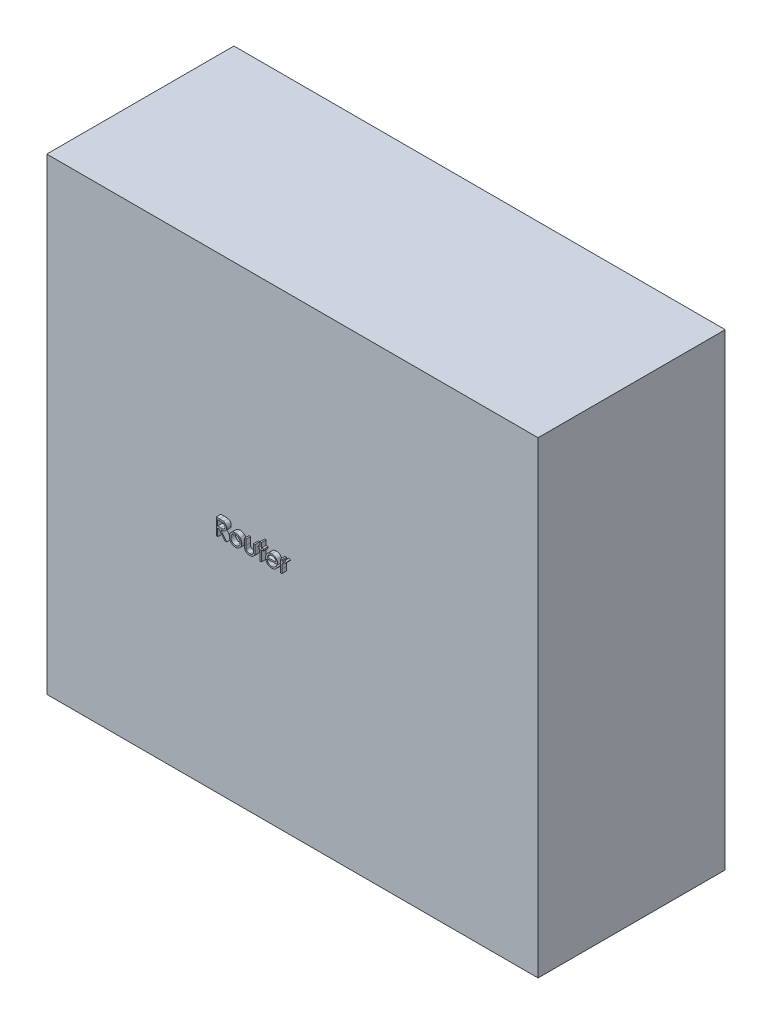
SolidWorks part; units mm, degrees
ref_plane "Front Plane" through (0, 0, 0) normal (0, 0, 1) x (1, 0, 0)
ref_plane "Top Plane" through (0, 0, 0) normal (0, 1, 0) x (1, 0, 0)
ref_plane "Right Plane" through (0, 0, 0) normal (1, 0, 0) x (0, 0, -1)
sketch "Sketch1" plane through (0, 0, 0) normal (0, 0, 1) x (1, 0, 0)
  line L5 (-52.5, -50) -> (52.5, -50)
  line L6 (-52.5, -50) -> (-52.5, 50)
  line L7 (-52.5, 50) -> (52.5, 50)
  line L8 (52.5, -50) -> (52.5, 50)
  line L9 (0, 50) -> (0, -50) construction
  line L10 (-52.5, 0) -> (52.5, 0) construction
  point P0 (0, 0)
  dimension "D1" = 100
  dimension "D2" = 105
extrude "Boss-Extrude1" add sketch "Sketch1" along normal blind 40
sketch "Sketch3" plane through (0, 0, 40) normal (0, 0, 1) x (1, 0, 0)
sketch "Sketch4" plane through (0, 0, 40) normal (0, 0, 1) x (1, 0, 0)
  text T0 "Router"
extrude "Boss-Extrude2" add sketch "Sketch4" along normal blind 1
